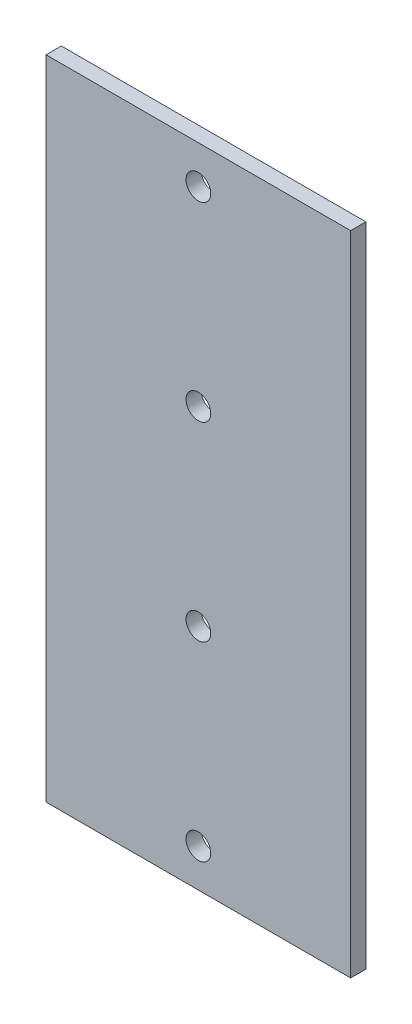
SolidWorks part; units mm, degrees
ref_plane "Piano frontale" through (0, 0, 0) normal (0, 0, 1) x (1, 0, 0)
ref_plane "Piano superiore" through (0, 0, 0) normal (0, 1, 0) x (1, 0, 0)
ref_plane "Piano destro" through (0, 0, 0) normal (1, 0, 0) x (0, 0, -1)
sketch "Schizzo1" plane through (0, 0, 0) normal (0, 0, 1) x (1, 0, 0)
  line L1 (-20, -42.5) -> (20, -42.5)
  line L2 (-20, -42.5) -> (-20, 42.5)
  line L3 (-20, 42.5) -> (20, 42.5)
  line L4 (20, -42.5) -> (20, 42.5)
  line L5 (-20, -42.5) -> (20, 42.5) construction
  line L6 (-20, 42.5) -> (20, -42.5) construction
  point P0 (0, 0)
  dimension "D1" = 40
  dimension "D2" = 85
extrude "Estrusione-Estrusione1" add sketch "Schizzo1" along normal mid plane 2
sketch "Schizzo2" plane through (0, 0, -1) normal (0, 0, -1) x (-1, 0, 0)
  line L0 (-20, 42.5) -> (20, 42.5) construction
  line L1 (0, 1.1) -> (0, -1.1) construction
  circle A0 centre (0, 37.5) radius 1.625
  point P4 (0, 0)
  dimension "D1" = 5
  dimension "D2" = 3.25
extrude "Taglio-Estrusione1" cut sketch "Schizzo2" against normal blind 2
pattern_linear "Ripetizione a L1" count 4 spacing 25 along (0, -1, 0) of "Taglio-Estrusione1"
